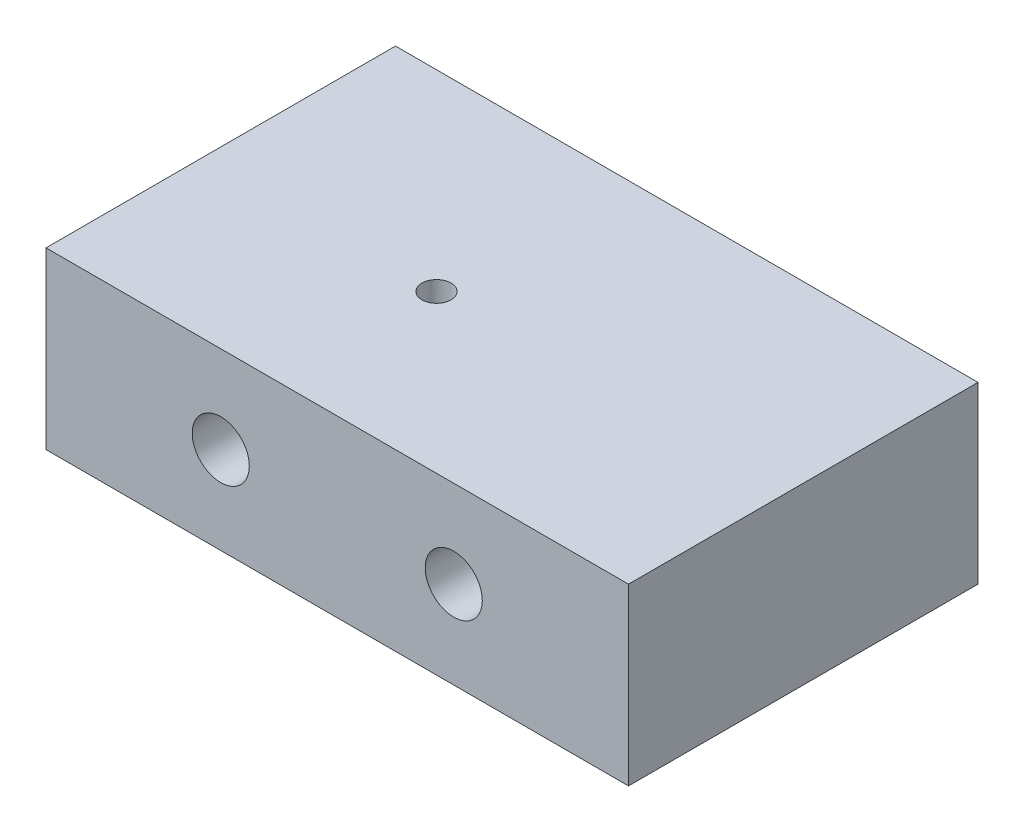
SolidWorks part; units mm, degrees
ref_plane "Front Plane" through (0, 0, 0) normal (0, 0, 1) x (1, 0, 0)
ref_plane "Top Plane" through (0, 0, 0) normal (0, 1, 0) x (1, 0, 0)
ref_plane "Right Plane" through (0, 0, 0) normal (1, 0, 0) x (0, 0, -1)
sketch "Sketch1" plane through (0, 0, 0) normal (0, 1, 0) x (1, 0, 0)
  line L0 (25, 0) -> (25, 30) construction
  line L1 (0, 0) -> (50, 0)
  line L2 (0, 0) -> (0, 30)
  line L3 (0, 30) -> (50, 30)
  line L4 (50, 0) -> (50, 30)
  dimension "D1" = 50
  dimension "D2" = 30
extrude "Boss-Extrude1" add sketch "Sketch1" along normal blind 15
sketch "Sketch2" plane through (0, 0, 0) normal (0, 0, 1) x (1, 0, 0)
  line L0 (0, 7.5) -> (50, 7.5) construction
  line L1 (0, 15) -> (0, 0) construction
  line L2 (50, 15) -> (50, 0) construction
  line L3 (25, 0) -> (25, 15) construction
  line L4 (0, 0) -> (50, 0) construction
  line L5 (0, 15) -> (50, 15) construction
  circle A0 centre (35, 7.5) radius 2.45
  circle A1 centre (15, 7.5) radius 2.45
  point P16 (0, 0)
  point P17 (0, 0)
  point P18 (35, 7.5)
  dimension "D1" = 4.9
  dimension "D3" = 4.9
  dimension "D2" = 20
extrude "Cut-Extrude1" cut sketch "Sketch2" against normal through all
sketch "Sketch3" plane through (0, 15, 0) normal (0, 1, 0) x (1, 0, 0)
  line L0 (0, 19.5) -> (50, 19.5) construction
  line L1 (0, 30) -> (0, 0) construction
  line L2 (50, 0) -> (50, 30) construction
  line L3 (0, 0) -> (50, 0) construction
  line L4 (25, 30) -> (25, 0) construction
  line L6 (50, 30) -> (0, 30) construction
  line L7 (25, 13.519) -> (20, 13.519) construction
  circle A0 centre (20, 13.519) radius 1.25
  dimension "D3" = 2.5
  dimension "D1" = 19.5
  dimension "D2" = 5
extrude "Cut-Extrude2" cut sketch "Sketch3" against normal through all contours A0
